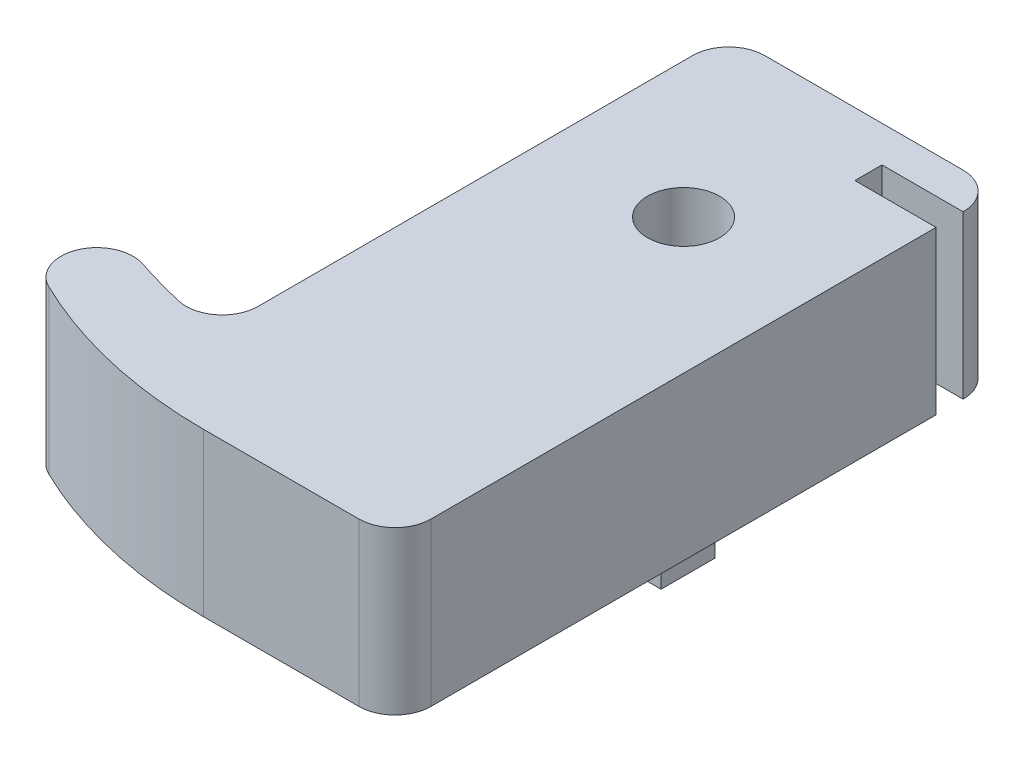
SolidWorks part; units mm, degrees
ref_plane "前视基准面" through (0, 0, 0) normal (0, 0, 1) x (1, 0, 0)
ref_plane "上视基准面" through (0, 0, 0) normal (0, 1, 0) x (1, 0, 0)
ref_plane "右视基准面" through (0, 0, 0) normal (1, 0, 0) x (0, 0, -1)
other "Configuration Table"
sketch "草图1" plane through (0, 0, 0) normal (0, 1, 0) x (1, 0, 0)
  line L0 (-2.3828, 33.5) -> (8.6172, 33.5)
  line L1 (10.6172, 31.5) -> (10.6172, 2)
  line L2 (8.6172, 0) -> (0, 0)
  line L5 (-4.3828, 7.4211) -> (-4.3828, 31.5)
  arc A0 (0, 0) -> (-11.1311, 2.5577) centre (0, 25.5) cw
  arc A1 (-6.8364, 5.4732) -> (-9.6333, 6.257) centre (0.5711, 37.2861) cw
  arc A2 (-11.1311, 2.5577) -> (-9.6333, 6.257) centre (-10.2581, 4.3571) cw
  arc A3 (-6.8364, 5.4732) -> (-4.3828, 7.4211) centre (-6.3828, 7.4211) ccw
  arc A4 (10.6172, 2) -> (8.6172, 0) centre (8.6172, 2) cw
  arc A5 (8.6172, 33.5) -> (10.6172, 31.5) centre (8.6172, 31.5) cw
  arc A6 (-2.3828, 33.5) -> (-4.3828, 31.5) centre (-2.3828, 31.5) ccw
  circle A7 centre (3.1172, 23.5) radius 2
  point P15 (10.6172, 0)
  point P18 (10.6172, 33.5)
  point P21 (-4.3828, 33.5)
  point P24 (3.1172, 33.5)
  dimension "D5" = 25.5
  dimension "D3" = 2
  dimension "D4" = 2
  dimension "D6" = 4
  dimension "D1" = 15
  dimension "D2" = 33.5
  dimension "D7" = 10
  dimension "D8" = 8.6172
extrude "凸台-拉伸1" add sketch "草图1" along normal blind 9
sketch "草图3" plane through (0, 9, 0) normal (0, 1, 0) x (1, 0, 0)
  line L0 (-4.3828, 31.5) -> (-4.3828, 7.4211) construction
  line L1 (-3.6328, 18.5) -> (-1.1328, 18.5)
  line L2 (-3.6328, 18.5) -> (-3.6328, 15.5)
  line L3 (-3.6328, 15.5) -> (-1.1328, 15.5)
  line L4 (-1.1328, 18.5) -> (-1.1328, 15.5)
  line L5 (3.1172, 23.5) -> (3.1172, 23.4622) construction
  line L6 (7.3672, 18.5) -> (7.3672, 15.5)
  line L7 (9.8672, 15.5) -> (7.3672, 15.5)
  line L8 (9.8672, 18.5) -> (9.8672, 15.5)
  line L9 (9.8672, 18.5) -> (7.3672, 18.5)
  circle A0 centre (3.1172, 23.5) radius 2 construction
  circle A1 centre (3.1172, 23.5) radius 2 construction
  dimension "D1" = 2.5
  dimension "D2" = 3
  dimension "D3" = 0.75
  dimension "D4" = 5
extrude "凸台-拉伸2" add sketch "草图3" along normal blind 1.5
sketch "草图5" plane through (0, 9, 0) normal (0, 1, 0) x (1, 0, 0)
  line L0 (8.6172, 33.5) -> (-2.3828, 33.5) construction
  line L1 (-2.3828, 31.5) -> (10.6172, 31.5)
  line L2 (-2.3828, 31.5) -> (-2.3828, 30)
  line L3 (-2.3828, 30) -> (10.6172, 30)
  line L4 (10.6172, 31.5) -> (10.6172, 30)
  line L5 (10.6172, 2) -> (10.6172, 31.5) construction
  dimension "D1" = 1.5
  dimension "D2" = 13
  dimension "D3" = 2
extrude "切除-拉伸1" cut sketch "草图5" against normal up to next
sketch "草图7" plane through (0, 0, 0) normal (0, -1, 0) x (1, 0, 0)
  line L0 (10.6172, -31.5) -> (-2.3828, -31.5) construction
  line L1 (-2.3828, -31.5) -> (-2.3828, -30) construction
  line L2 (-2.3828, -30) -> (10.6172, -30) construction
  line L3 (6.1172, -31.5) -> (-2.3828, -31.5)
  line L4 (-2.3828, -31.5) -> (-2.3828, -30)
  line L5 (-2.3828, -30) -> (6.1172, -30)
  line L6 (5.1172, -23.5) -> (5.1172, -31.5) construction
  line L7 (6.1172, -31.5) -> (6.1172, -30)
  circle A0 centre (3.1172, -23.5) radius 2 construction
  dimension "D1" = 1
extrude "凸台-拉伸3" add sketch "草图7" against normal blind 4
mirror "镜向8" about plane through (0, 0, -25.5) normal (0, -1, 0) of bodies 109
sketch "草图9" plane through (0, 0, 0) normal (0, 1, 0) x (1, 0, 0)
  line L1 (-24.5545, 37.01) -> (24.9915, 37.01)
  line L2 (-24.5545, 37.01) -> (-24.5545, -5.1983)
  line L3 (-24.5545, -5.1983) -> (24.9915, -5.1983)
  line L4 (24.9915, 37.01) -> (24.9915, -5.1983)
extrude "切除-拉伸3" cut sketch "草图9" along normal through all
